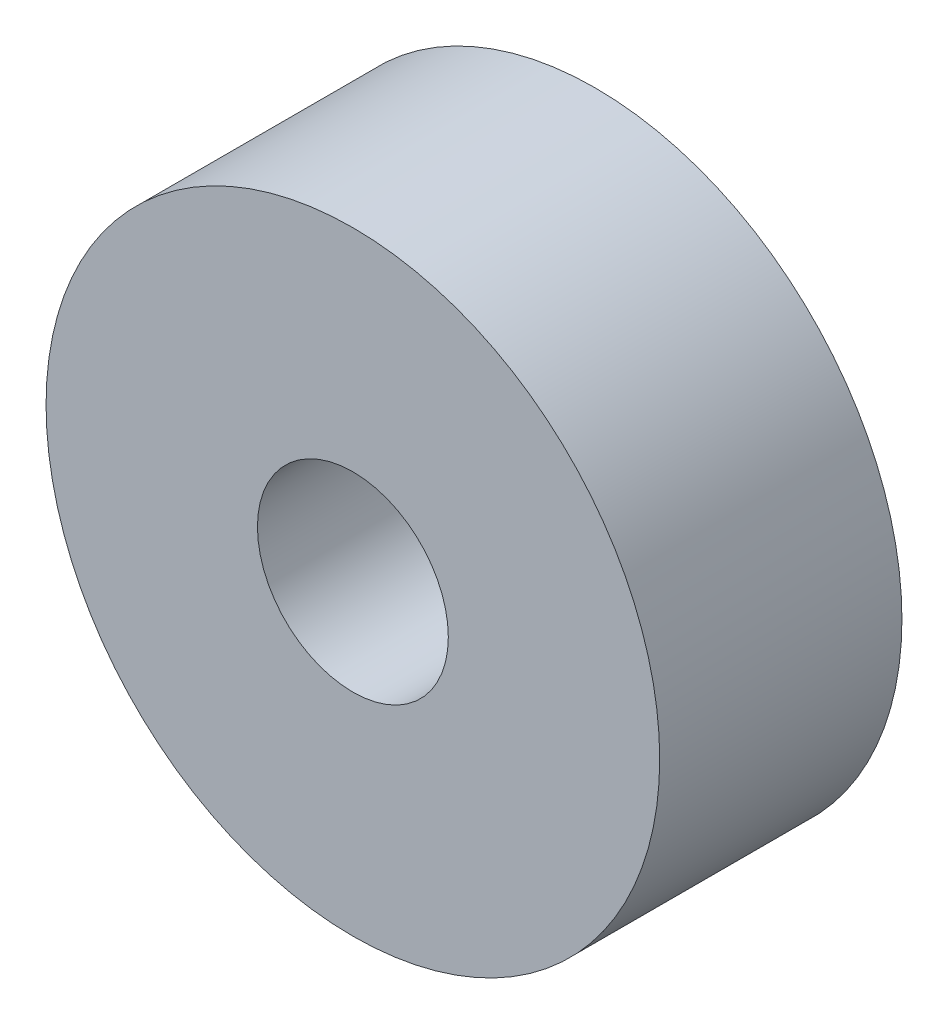
SolidWorks part; units mm, degrees
ref_plane "Front Plane" through (0, 0, 0) normal (0, 0, 1) x (1, 0, 0)
ref_plane "Top Plane" through (0, 0, 0) normal (0, 1, 0) x (1, 0, 0)
ref_plane "Right Plane" through (0, 0, 0) normal (1, 0, 0) x (0, 0, -1)
sketch "Sketch1" plane through (0, 0, 0) normal (0, 0, 1) x (1, 0, 0)
  circle A0 centre (0, 0) radius 9.5
  dimension "D1" = 19
extrude "Main Extrude" add sketch "Sketch1" along normal blind 7.5
sketch "Sketch2" plane through (0, 0, 7.5) normal (0, 0, 1) x (1, 0, 0)
  circle A0 centre (0, 0) radius 2.955
  dimension "D1" = 5.91
ref_plane "Halfway front plane" through (0, 0, 3) normal (0, 0, 1) x (1, 0, 0)
extrude "Cut-Extrude1" cut sketch "Sketch2" against normal blind 10
